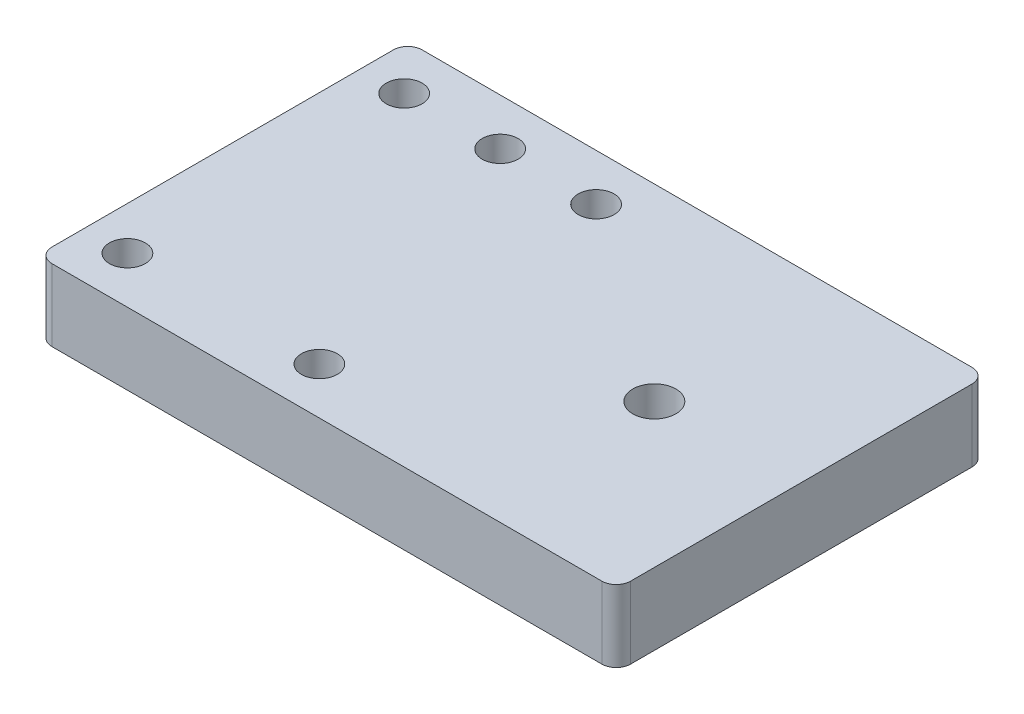
SolidWorks part; units mm, degrees
ref_plane "Front Plane" through (0, 0, 0) normal (0, 0, 1) x (1, 0, 0)
ref_plane "Top Plane" through (0, 0, 0) normal (0, 1, 0) x (1, 0, 0)
ref_plane "Right Plane" through (0, 0, 0) normal (1, 0, 0) x (0, 0, -1)
sketch "Sketch1" plane through (0, 0, 0) normal (0, 1, 0) x (1, 0, 0)
  line L1 (-40.25, -25.75) -> (40.25, -25.75)
  line L2 (-40.25, -25.75) -> (-40.25, 25.75)
  line L3 (-40.25, 25.75) -> (40.25, 25.75)
  line L4 (40.25, -25.75) -> (40.25, 25.75)
  line L5 (-40.25, -25.75) -> (40.25, 25.75) construction
  line L6 (-40.25, 25.75) -> (40.25, -25.75) construction
  point P0 (0, 0)
  dimension "D1" = 51.5
  dimension "D2" = 80.5
extrude "Boss-Extrude1" add sketch "Sketch1" along normal blind 10
ref_plane "Plane1" through (-20.9, 0, 0) normal (-1, 0, 0) x (0, 0, 1)
sketch "Sketch2" plane through (0, 10, 0) normal (0, 1, 0) x (1, 0, 0)
  line L0 (-40.25, 25.75) -> (-40.25, -25.75) construction
  circle A0 centre (-34.25, 19.25) radius 2.5
  dimension "D1" = 5
  dimension "D2" = 19.25
  dimension "D3" = 6
extrude "Cut-Extrude1" cut sketch "Sketch2" against normal through all
mirror "Mirror1" about plane through (-20.9, 0, 0) normal (-1, 0, 0) of "Cut-Extrude1"
mirror "Mirror2" about plane through (0, 0, 0) normal (0, 0, 1) of "Mirror1", "Cut-Extrude1"
sketch "Sketch3" plane through (0, 10, 0) normal (0, 1, 0) x (1, 0, 0)
  line L0 (-20.9, 5.5) -> (-20.9, -5.5) construction
  circle A0 centre (-20.9, 19.25) radius 2.5
  dimension "D1" = 5
  dimension "D2" = 19.25
extrude "Cut-Extrude2" cut sketch "Sketch3" against normal through all
sketch "Sketch4" plane through (0, 10, 0) normal (0, 1, 0) x (1, 0, 0)
  line L0 (-40.25, -25.75) -> (40.25, -25.75) construction
  line L1 (40.25, -25.75) -> (40.25, 25.75) construction
  circle A0 centre (20.25, -0.45) radius 3
  dimension "D1" = 6
  dimension "D2" = 25.3
  dimension "D3" = 20
extrude "Cut-Extrude3" cut sketch "Sketch4" against normal through all
fillet "Fillet1" radius 2 4 edges at (40.25, 5, -25.75) (40.25, 5, 25.75) (-40.25, 5, 25.75) (-40.25, 5, -25.75)
